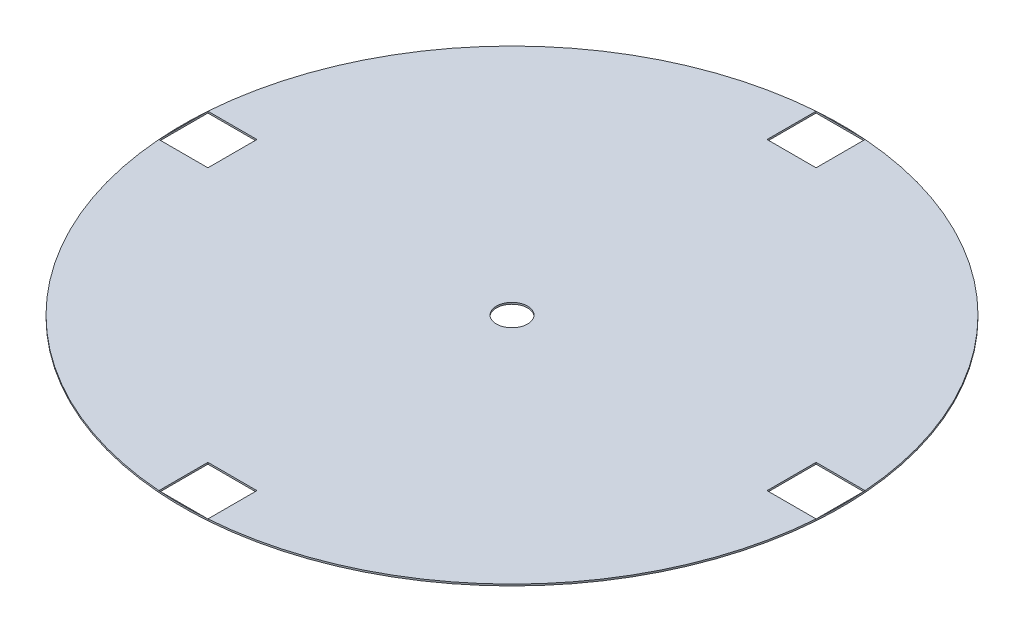
SolidWorks part; units mm, degrees
ref_plane "Alzado" through (0, 0, 0) normal (0, 0, 1) x (1, 0, 0)
ref_plane "Planta" through (0, 0, 0) normal (0, 1, 0) x (1, 0, 0)
ref_plane "Vista lateral" through (0, 0, 0) normal (1, 0, 0) x (0, 0, -1)
sketch "Croquis1" plane through (0, 0, 0) normal (0, 1, 0) x (1, 0, 0)
  circle A0 centre (0, 0) radius 403.28
  circle A1 centre (0, 0) radius 19.05
  dimension "D1" = 38.1
  dimension "D2" = 806.56
extrude "Saliente-Extruir1" add sketch "Croquis1" along normal blind 2
sketch "Croquis2" plane through (0, 2, 0) normal (0, 1, 0) x (1, 0, 0)
  line L0 (402.1626, 30) -> (317.3098, 30)
  line L1 (317.3098, 30) -> (317.3098, -30)
  line L2 (317.3098, -30) -> (402.1626, -30)
  line L3 (402.1626, -30) -> (402.1626, 30)
  line L4 (0, 0) -> (317.3098, 0) construction
  line L5 (30, -402.1626) -> (30, -317.3098)
  line L6 (30, -317.3098) -> (-30, -317.3098)
  line L7 (-30, -317.3098) -> (-30, -402.1626)
  line L8 (-30, -402.1626) -> (30, -402.1626)
  line L9 (-402.1626, -30) -> (-317.3098, -30)
  line L10 (-317.3098, -30) -> (-317.3098, 30)
  line L11 (-317.3098, 30) -> (-402.1626, 30)
  line L12 (-402.1626, 30) -> (-402.1626, -30)
  line L13 (-30, 402.1626) -> (-30, 317.3098)
  line L14 (-30, 317.3098) -> (30, 317.3098)
  line L15 (30, 317.3098) -> (30, 402.1626)
  line L16 (30, 402.1626) -> (-30, 402.1626)
  line L17 (0, 0) -> (0, 317.3098) construction
  line L18 (0, 0) -> (-317.3098, 0) construction
  line L19 (0, 0) -> (0, -317.3098) construction
  circle A0 centre (0, 0) radius 403.28 construction
  point P10 (402.1626, 0)
  point P19 (0, -402.1626)
  point P24 (-402.1626, 0)
  point P29 (0, 402.1626)
  point P30 (0, 0)
  dimension "D1" = 84.8528
  dimension "D2" = 60
  dimension "D3" = 4
sketch "Croquis3" plane through (0, 2, 0) normal (0, 1, 0) x (1, 0, 0)
  line L0 (402.1626, 30) -> (342.1626, 30)
  line L1 (342.1626, 30) -> (342.1626, -30)
  line L2 (342.1626, -30) -> (402.1626, -30)
  line L3 (402.1626, -30) -> (402.1626, 30)
  line L4 (0, 0) -> (342.1626, 0) construction
  line L19 (30, -402.1626) -> (30, -342.1626)
  line L20 (30, -342.1626) -> (-30, -342.1626)
  line L21 (-30, -342.1626) -> (-30, -402.1626)
  line L22 (-30, -402.1626) -> (30, -402.1626)
  line L23 (0, 0) -> (0, -342.1626) construction
  line L24 (-402.1626, -30) -> (-342.1626, -30)
  line L25 (-342.1626, -30) -> (-342.1626, 30)
  line L26 (-342.1626, 30) -> (-402.1626, 30)
  line L27 (-402.1626, 30) -> (-402.1626, -30)
  line L28 (0, 0) -> (-342.1626, 0) construction
  line L29 (-30, 402.1626) -> (-30, 342.1626)
  line L30 (-30, 342.1626) -> (30, 342.1626)
  line L31 (30, 342.1626) -> (30, 402.1626)
  line L32 (30, 402.1626) -> (-30, 402.1626)
  line L33 (0, 0) -> (0, 342.1626) construction
  circle A2 centre (0, 0) radius 403.28 construction
  point P8 (402.1626, 0)
  point P19 (0, -402.1626)
  point P25 (-402.1626, 0)
  point P34 (0, 402.1626)
  point P35 (0, 0)
  dimension "D1" = 806.56
  dimension "D2" = 60
  dimension "D3" = 4
  dimension "D4" = 60
extrude "Cortar-Extruir1" cut sketch "Croquis3" against normal through all
